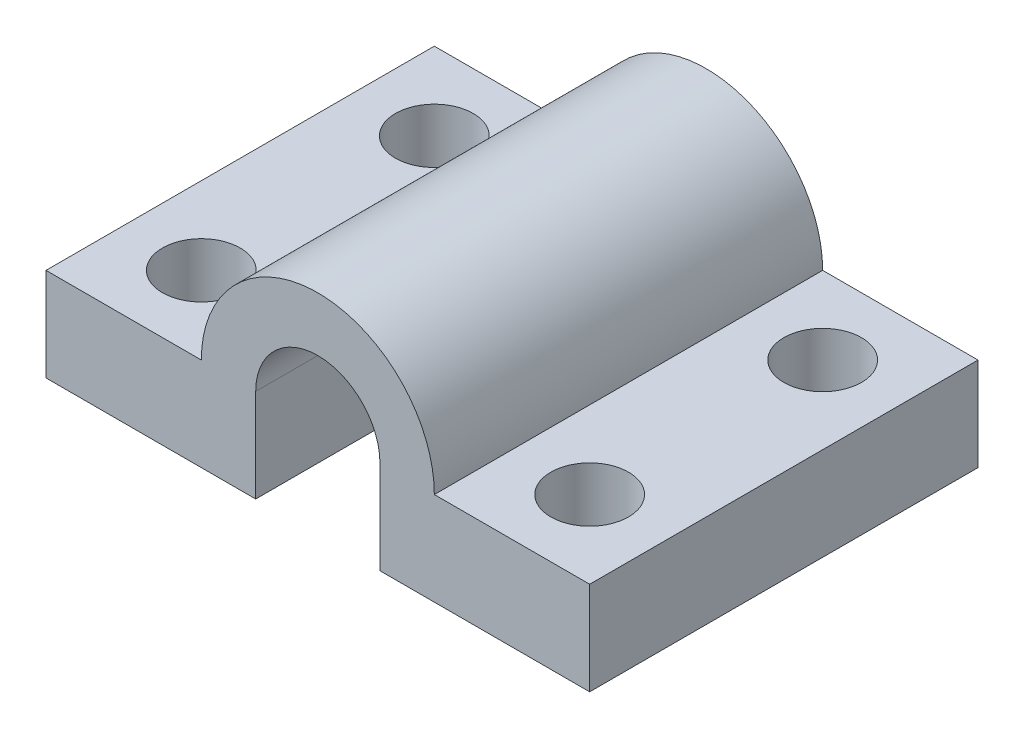
SolidWorks part; units mm, degrees
ref_plane "Front Plane" through (0, 0, 0) normal (0, 0, 1) x (1, 0, 0)
ref_plane "Top Plane" through (0, 0, 0) normal (0, 1, 0) x (1, 0, 0)
ref_plane "Right Plane" through (0, 0, 0) normal (1, 0, 0) x (0, 0, -1)
sketch "Sketch1" plane through (0, 0, 0) normal (0, 1, 0) x (1, 0, 0)
  line L1 (-12.2135, 8.3854) -> (22.7865, 8.3854)
  line L2 (-12.2135, 8.3854) -> (-12.2135, -16.6146)
  line L3 (-12.2135, -16.6146) -> (22.7865, -16.6146)
  line L4 (22.7865, 8.3854) -> (22.7865, -16.6146)
  dimension "D1" = 35
  dimension "D2" = 25
extrude "Boss-Extrude1" add sketch "Sketch1" along normal blind 6
sketch "Sketch2" plane through (0, 6, 0) normal (0, 1, 0) x (1, 0, 0)
  line L0 (-12.2135, 8.3854) -> (-12.2135, -16.6146) construction
  line L1 (22.7865, 8.3854) -> (-12.2135, 8.3854) construction
  line L2 (22.7865, -16.6146) -> (22.7865, 8.3854) construction
  circle A1 centre (-7.2135, -11.6146) radius 2.5
  circle A2 centre (17.7865, 3.3854) radius 2.5
  circle A3 centre (17.7865, -11.6146) radius 2.5
  circle A4 centre (-7.2135, 3.3854) radius 2.5
  dimension "D1" = 5
  dimension "D2" = 5
  dimension "D3" = 25
  dimension "D4" = 15
  dimension "D5" = 5
  dimension "D6" = 5
  dimension "D7" = 25
  dimension "D8" = 15
extrude "Cut-Extrude1" cut sketch "Sketch2" against normal blind 6
sketch "Sketch3" plane through (0, 6, 0) normal (0, 1, 0) x (1, 0, 0)
  line L0 (22.7865, 8.3854) -> (-12.2135, 8.3854) construction
  line L1 (5.2865, 8.3854) -> (12.7865, 8.3854)
  line L2 (5.2865, 8.3854) -> (5.2865, -16.6146)
  line L3 (5.2865, -16.6146) -> (12.7865, -16.6146)
  line L4 (12.7865, 8.3854) -> (12.7865, -16.6146)
  line L5 (-12.2135, -16.6146) -> (22.7865, -16.6146) construction
  line L6 (22.7865, -16.6146) -> (22.7865, 8.3854) construction
  dimension "D1" = 10
  dimension "D2" = 17.5
revolve "Revolve1" add sketch "Sketch3" angle 180 about L2
sketch "Sketch4" plane through (0, 0, 16.6146) normal (0, 0, 1) x (1, 0, 0)
  line L0 (22.7865, 6) -> (22.7865, 0) construction
  line L1 (-12.2135, 0) -> (22.7865, 0) construction
  line L3 (1.2865, 6) -> (9.2865, 6)
  line L4 (1.2865, 6) -> (1.2865, 0)
  line L5 (1.2865, 0) -> (9.2865, 0)
  line L6 (9.2865, 6) -> (9.2865, 0)
  circle A0 centre (5.2865, 6) radius 4
  line M1 (-12.2135, 0) -> (22.7865, 0)
  dimension "D1" = 17.5
  dimension "D2" = 6
extrude "Cut-Extrude2" cut sketch "Sketch4" against normal blind 36 contours L3 A0 | L3 A0 | A0 L4 L6 M1
